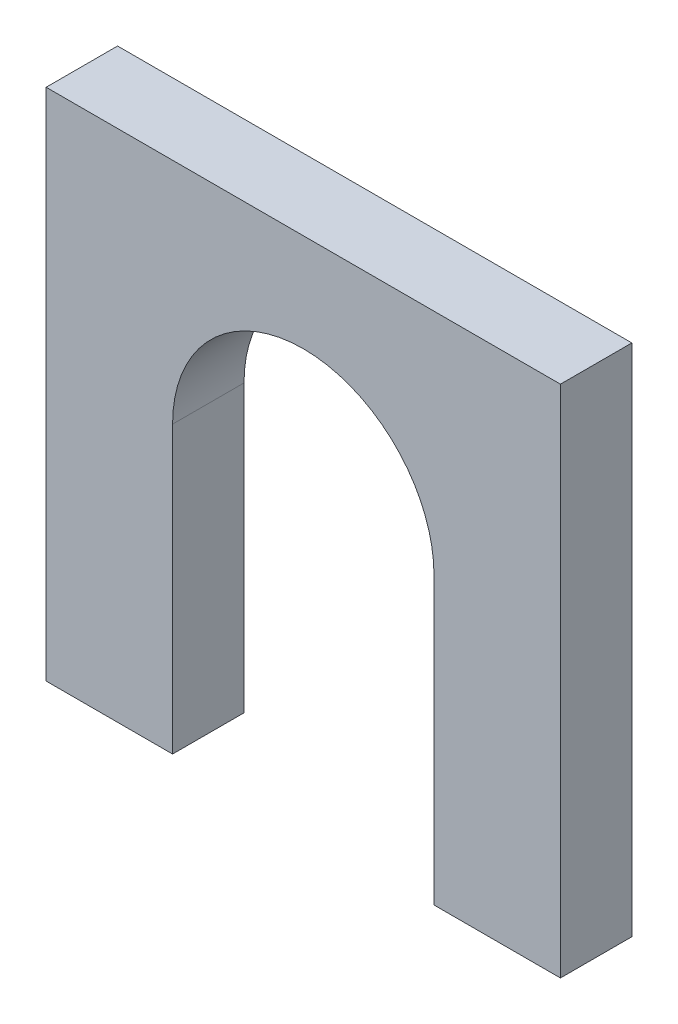
SolidWorks part; units mm, degrees
ref_plane "Front Plane" through (0, 0, 0) normal (0, 0, 1) x (1, 0, 0)
ref_plane "Top Plane" through (0, 0, 0) normal (0, 1, 0) x (1, 0, 0)
ref_plane "Right Plane" through (0, 0, 0) normal (1, 0, 0) x (0, 0, -1)
sketch "Sketch1" plane through (0, 0, 0) normal (0, 0, 1) x (1, 0, 0)
  line L0 (34.4805, 0) -> (45.72, 0)
  line L1 (0, 0) -> (11.2395, 0)
  line L2 (0, 0) -> (0, 45.72)
  line L3 (0, 45.72) -> (45.72, 45.72)
  line L4 (45.72, 0) -> (45.72, 45.72)
  line L5 (0, 25.4) -> (11.2395, 25.4) construction
  line L6 (22.86, 37.0205) -> (22.86, 0) construction
  line L7 (11.2395, 25.4) -> (11.2395, 0)
  line L8 (34.4805, 25.4) -> (45.72, 25.4) construction
  line L9 (34.4805, 25.4) -> (34.4805, 0)
  line L10 (11.2395, 0) -> (34.4805, 0) construction
  arc A0 (34.4805, 25.4) -> (11.2395, 25.4) centre (22.86, 25.4) ccw
  point P7 (11.2395, 25.4)
  point P8 (34.4805, 25.4)
  dimension "D3" = 37.0205
  dimension "D5" = 23.241
  dimension "D1" = 45.72
  dimension "D2" = 45.72
extrude "Boss-Extrude1" add sketch "Sketch1" along normal blind 6.35
